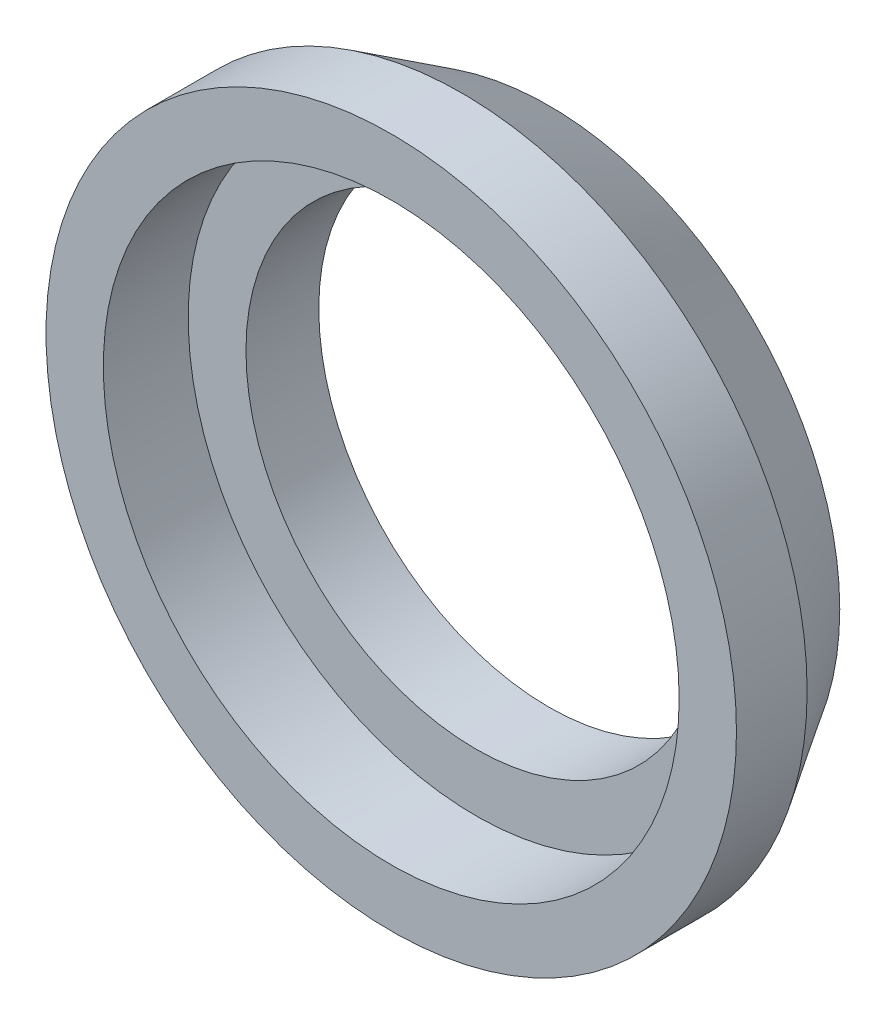
SolidWorks part; units mm, degrees
material "Delrin 2700 NC010, Low Viscosity Acetal Copolymer (SS)"
ref_plane "Front Plane" through (0, 0, 0) normal (0, 0, 1) x (1, 0, 0)
ref_plane "Top Plane" through (0, 0, 0) normal (0, 1, 0) x (1, 0, 0)
ref_plane "Right Plane" through (0, 0, 0) normal (1, 0, 0) x (0, 0, -1)
sketch "Sketch1" plane through (0, 0, 0) normal (0, 0, 1) x (1, 0, 0)
  circle A0 centre (0, 0) radius 9.525
  dimension "D1" = 19.05
extrude "Boss-Extrude1" add sketch "Sketch1" along normal mid plane 9
sketch "Sketch2" plane through (0, 0, 4.5) normal (0, 0, 1) x (1, 0, 0)
  circle A0 centre (0, 0) radius 6.35
  dimension "D1" = 12.7
extrude "Cut-Extrude1" cut sketch "Sketch2" against normal through all
chamfer "Chamfer1" distance 1.5 angle 58 2 edges at (9.525, 0, -4.5) (9.525, 0, 4.5)
sketch "Sketch3" plane through (0, 0, 4.5) normal (0, 0, 1) x (1, 0, 0)
  circle A0 centre (0, 0) radius 7.874
  dimension "D1" = 15.748
extrude "Cut-Extrude2" cut sketch "Sketch3" against normal blind 2.011
sketch "Sketch4" plane through (0, 0, 2.489) normal (0, 0, 1) x (1, 0, 0)
  circle A0 centre (0, 0) radius 7.9438
  dimension "D1" = 15.8877
extrude "Cut-Extrude3" cut sketch "Sketch4" against normal blind 4.98
sketch "Sketch5" plane through (0, 0, 0) normal (0, 0, 1) x (1, 0, 0)
  circle A0 centre (0, 0) radius 24.2374
extrude "Cut-Extrude4" cut sketch "Sketch5" along normal through all
sketch "Sketch6" plane through (0, 0, 0) normal (0, 0, 1) x (1, 0, 0)
  circle A0 centre (0, 0) radius 11.6142
extrude "Cut-Extrude5" cut sketch "Sketch6" against normal blind 0.15
